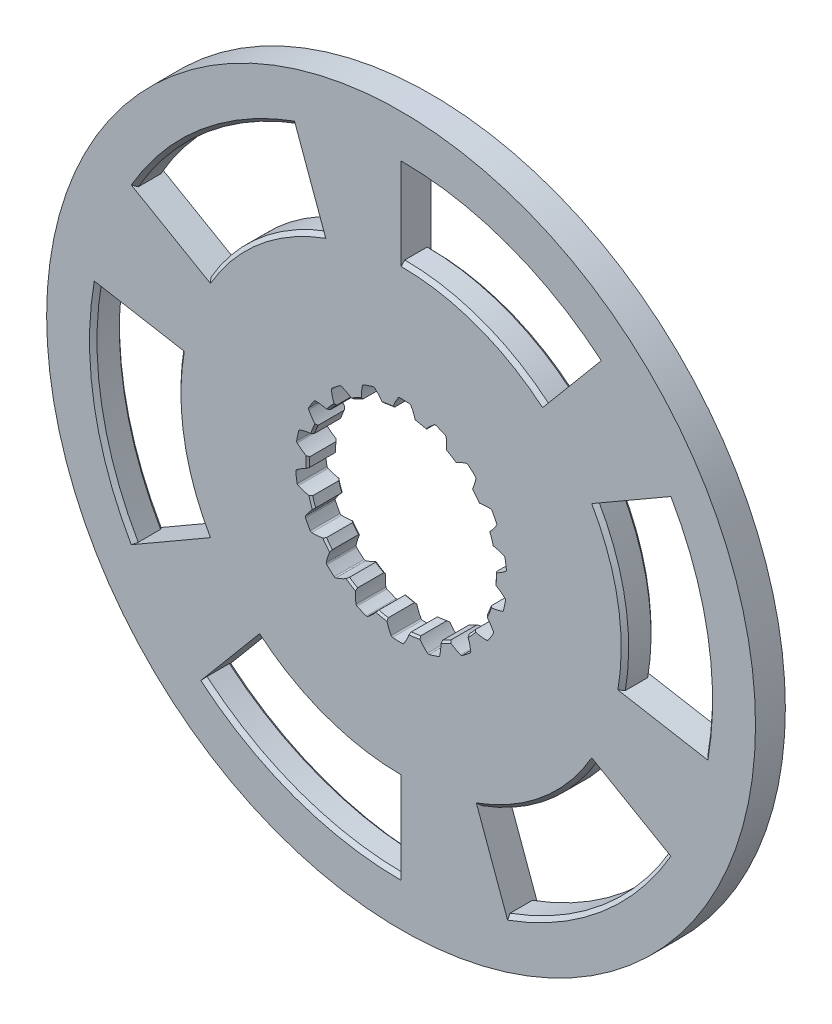
SolidWorks part; units mm, degrees
material "1.6587 (18CrNiMo7-6)"
ref_plane "Front Plane" through (0, 0, 0) normal (0, 0, 1) x (1, 0, 0)
ref_plane "Top Plane" through (0, 0, 0) normal (0, 1, 0) x (1, 0, 0)
ref_plane "Right Plane" through (0, 0, 0) normal (1, 0, 0) x (0, 0, -1)
sketch "Sketch1" plane through (0, 0, 0) normal (0, 0, 1) x (1, 0, 0)
  line L0 (-20.5212, 56.3816) -> (-28.2167, 77.5246)
  line L1 (0, 60) -> (0, 82.5)
  line L2 (51.9615, 30) -> (71.4471, 41.25)
  line L3 (38.5673, 45.9627) -> (53.03, 63.1987)
  line L4 (51.9615, -30) -> (71.4471, -41.25)
  line L5 (59.0885, -10.4189) -> (81.2466, -14.326)
  line L6 (0, -60) -> (0, -82.5)
  line L7 (20.5212, -56.3816) -> (28.2167, -77.5246)
  line L8 (-51.9615, -30) -> (-71.4471, -41.25)
  line L9 (-38.5673, -45.9627) -> (-53.03, -63.1987)
  line L10 (-51.9615, 30) -> (-71.4471, 41.25)
  line L11 (-59.0885, 10.4189) -> (-81.2466, 14.326)
  circle A0 centre (0, 0) radius 95
  arc A1 (-28.2167, 77.5246) -> (-71.4471, 41.25) centre (0, 0) ccw
  arc A2 (-20.5212, 56.3816) -> (-51.9615, 30) centre (0, 0) ccw
  arc A3 (-59.0885, 10.4189) -> (-51.9615, -30) centre (0, 0) ccw
  arc A4 (-81.2466, 14.326) -> (-71.4471, -41.25) centre (0, 0) ccw
  arc A5 (-38.5673, -45.9627) -> (0, -60) centre (0, 0) ccw
  arc A6 (-53.03, -63.1987) -> (0, -82.5) centre (0, 0) ccw
  arc A7 (20.5212, -56.3816) -> (51.9615, -30) centre (0, 0) ccw
  arc A8 (28.2167, -77.5246) -> (71.4471, -41.25) centre (0, 0) ccw
  arc A9 (59.0885, -10.4189) -> (51.9615, 30) centre (0, 0) ccw
  arc A10 (81.2466, -14.326) -> (71.4471, 41.25) centre (0, 0) ccw
  arc A11 (38.5673, 45.9627) -> (0, 60) centre (0, 0) ccw
  arc A12 (53.03, 63.1987) -> (0, 82.5) centre (0, 0) ccw
  point P20 (0, 0)
  dimension "D1" = 190
  dimension "D2" = 165
  dimension "D3" = 120
  dimension "D4" = 20
  dimension "D5" = 6
extrude "Boss-Extrude1" add sketch "Sketch1" along normal blind 8
sketch "Sketch2" plane through (0, 0, 8) normal (0, 0, 1) x (1, 0, 0)
  circle A0 centre (0, 0) radius 25.05
  dimension "D1" = 50.1
extrude "Cut-Extrude1" cut sketch "Sketch2" against normal blind 8
sketch "Sketch3" plane through (0, 0, 8) normal (0, 0, 1) x (1, 0, 0)
  line L0 (0, 0) -> (26.961, 1.4505) construction
  line L1 (0, 0) -> (38.0501, -1.2758) construction
  line L2 (0, 0) -> (37.7006, 5.3519) construction
  arc A0 (25.0462, 0.4359) -> (24.178, 6.5518) centre (0, 0) ccw
  circle A1 centre (0, 0) radius 27 construction
  arc A2 (28.2486, 2.3955) -> (27.7993, 5.5609) centre (0, 0) ccw
  spline S0 degree 4 poles (23.3827, 0) (23.3967, 0.0003) (23.436, 0.0018) (23.51, 0.0081) (23.6305, 0.0229) (23.7834, 0.0485) (23.9798, 0.0893) (24.2095, 0.1473) (24.4599, 0.2213) (24.7297, 0.3128) (24.9963, 0.4138) (25.2596, 0.5234) (25.5193, 0.6406) (25.8307, 0.7919) (26.1994, 0.9862) (26.6229, 1.2318) (27.0938, 1.532) (27.5628, 1.8603) (28.0151, 2.2018) (28.4605, 2.5672) (28.8832, 2.9353) (29.3095, 3.3379) (29.6966, 3.7198) (30.1151, 4.1692) (30.4485, 4.5382) (30.8715, 5.0472) (31.1162, 5.3543) (31.3965, 5.7212) (31.5178, 5.888) (31.5926, 5.9906) knots 0 0 0 0 0 0.005377 0.015084 0.028532 0.04661 0.064855 0.092111 0.119476 0.146842 0.174209 0.201575 0.228941 0.256307 0.307035 0.361767 0.4165 0.471232 0.525964 0.580697 0.635429 0.690161 0.744894 0.799626 0.854358 0.909091 0.954545 1 1 1 1 1 construction
  spline S1 degree 4 poles (25.0462, 0.4359) (25.0666, 0.4442) (25.153, 0.4794) (25.3044, 0.5437) (25.5193, 0.6406) (25.8307, 0.7919) (26.1994, 0.9862) (26.6229, 1.2318) (27.0938, 1.532) (27.566, 1.8626) (27.9082, 2.1211) (28.135, 2.3024) (28.2486, 2.3955) knots 0.165762 0.165762 0.165762 0.165762 0.165762 0.174209 0.201575 0.228941 0.256307 0.307035 0.361767 0.4165 0.471232 0.527454 0.527454 0.527454 0.527454 0.527454
  spline S2 degree 4 poles (24.178, 6.5518) (24.1999, 6.5496) (24.2926, 6.5398) (24.456, 6.5202) (24.6894, 6.4869) (25.0306, 6.4282) (25.4388, 6.3442) (25.9139, 6.2262) (26.4497, 6.069) (26.9953, 5.8828) (27.3959, 5.7298) (27.6642, 5.6187) (27.7993, 5.5609) knots 0.165762 0.165762 0.165762 0.165762 0.165762 0.174209 0.201575 0.228941 0.256307 0.307035 0.361767 0.4165 0.471232 0.527454 0.527454 0.527454 0.527454 0.527454
  dimension "D1" = 50.1
  dimension "D2" = 54
  dimension "D3" = 56.7
  dimension "D4" = 5
  dimension "D5" = 5
extrude "Cut-Extrude3" cut sketch "Sketch3" against normal blind 8
fillet "Fillet1" radius 0.48 2 edges at (28.2486, 2.3955, 4) (27.7993, 5.5609, 4)
chamfer "Chamfer1" distance 0.5 2 edges at (-24.8013, -3.5207, 0) (-24.8013, -3.5207, 8)
pattern_circular "CirPattern1" count 18 over 360 about axis through (0, 0, 0) along (0, 0, 1) of "Fillet1", "Cut-Extrude3"
chamfer "Chamfer2" distance 1 angle 45 24 edges at (-38.5673, 45.9627, 0) (-53.03, 63.1987, 0) (28.2167, 77.5246, 0) (20.5212, 56.3816, 0) (59.0885, 10.4189, 0) (81.2466, 14.326, 0) (38.5673, -45.9627, 0) (53.03, -63.1987, 0) (-20.5212, -56.3816, 0) (-28.2167, -77.5246, 0) (-81.2466, -14.326, 0) (-59.0885, -10.4189, 0) (-59.0885, -10.4189, 8) (-81.2466, -14.326, 8) (-20.5212, -56.3816, 8) (38.5673, -45.9627, 8) (-28.2167, -77.5246, 8) (53.03, -63.1987, 8) (81.2466, 14.326, 8) (59.0885, 10.4189, 8) (28.2167, 77.5246, 8) (20.5212, 56.3816, 8) (-53.03, 63.1987, 8) (-38.5673, 45.9627, 8)
